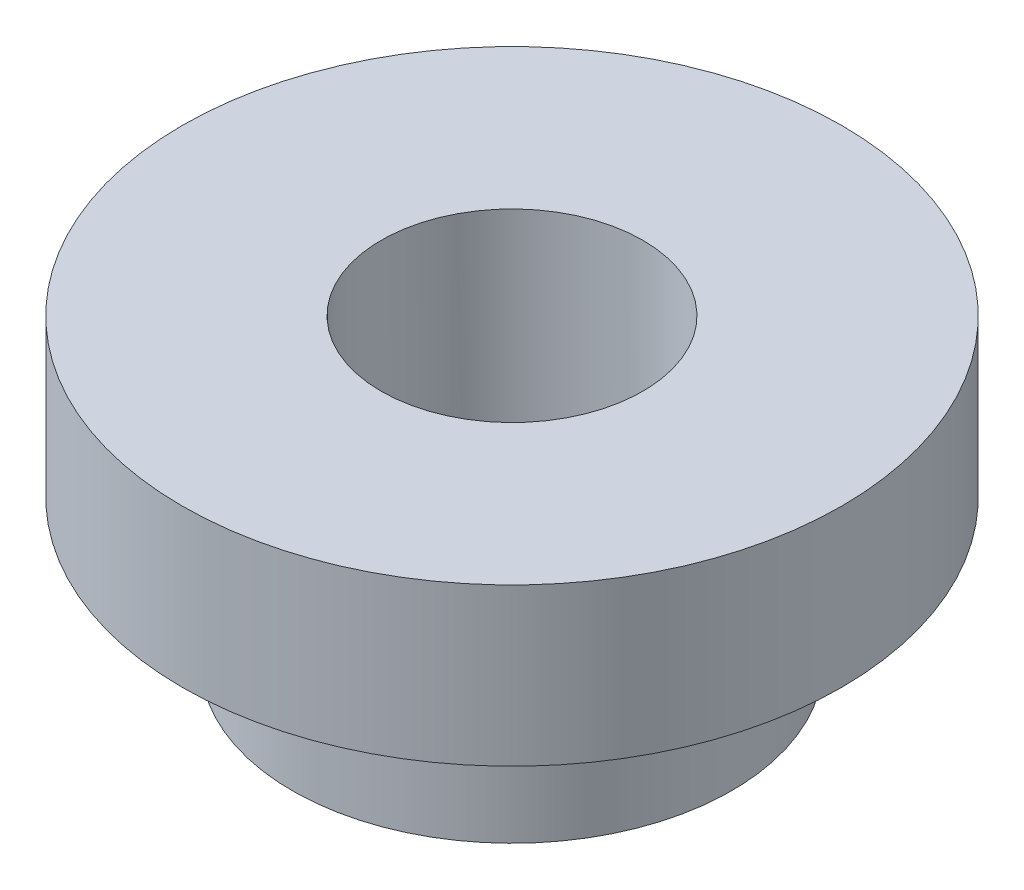
SolidWorks part; units mm, degrees
material "acero"
ref_plane "Alzado" through (0, 0, 0) normal (0, 0, 1) x (1, 0, 0)
ref_plane "Planta" through (0, 0, 0) normal (0, 1, 0) x (1, 0, 0)
ref_plane "Vista lateral" through (0, 0, 0) normal (1, 0, 0) x (0, 0, -1)
sketch "Croquis1" plane through (0, 0, 0) normal (0, 0, 1) x (1, 0, 0)
  line L0 (0, 0) -> (3.15, 0)
  line L1 (3.15, 0) -> (3.15, -1.5)
  line L2 (3.15, -1.5) -> (2.1, -1.5)
  line L3 (2.1, -1.5) -> (2.1, -2.88)
  line L4 (2.1, -2.88) -> (0, -2.88)
  line L5 (0, 0) -> (0, -2.88)
  dimension "D1" = 3.15
  dimension "D2" = 1.5
  dimension "D3" = 1.38
  dimension "D4" = 2.1
revolve "Revolución1" add sketch "Croquis1" angle 360 about L5
hole_wizard "Taladro roscado M31" positions "Croquis3" profile "Croquis2" tap size "M3" standard "Din"
sketch "Croquis3" plane through (0, 0, 0) normal (0, 1, 0) x (1, 0, 0)
  point P0 (0, 0)
sketch "Croquis2" plane through (0, 0, 0) normal (1, 0, 0) x (0, 0, 1)
  line L0 (0, 0) -> (0, 10.7511)
  line L1 (0, 10.7511) -> (1.25, 10)
  line L2 (1.25, 10) -> (1.25, 0)
  line L5 (1.25, 0) -> (0, 0)
  line L10 (0, 10.7511) -> (-1.25, 10) construction
  line L11 (0, -6.35) -> (0, 107.95) construction
  dimension "Diámetro de perforador para roscar" = 2.5
  dimension "Profundidad de perforador para roscar" = 10
  dimension "Ángulo de perforador" = 118
cosmetic thread "Rosca de taladro1" parameters "D1"=2.47, "D2"=3
